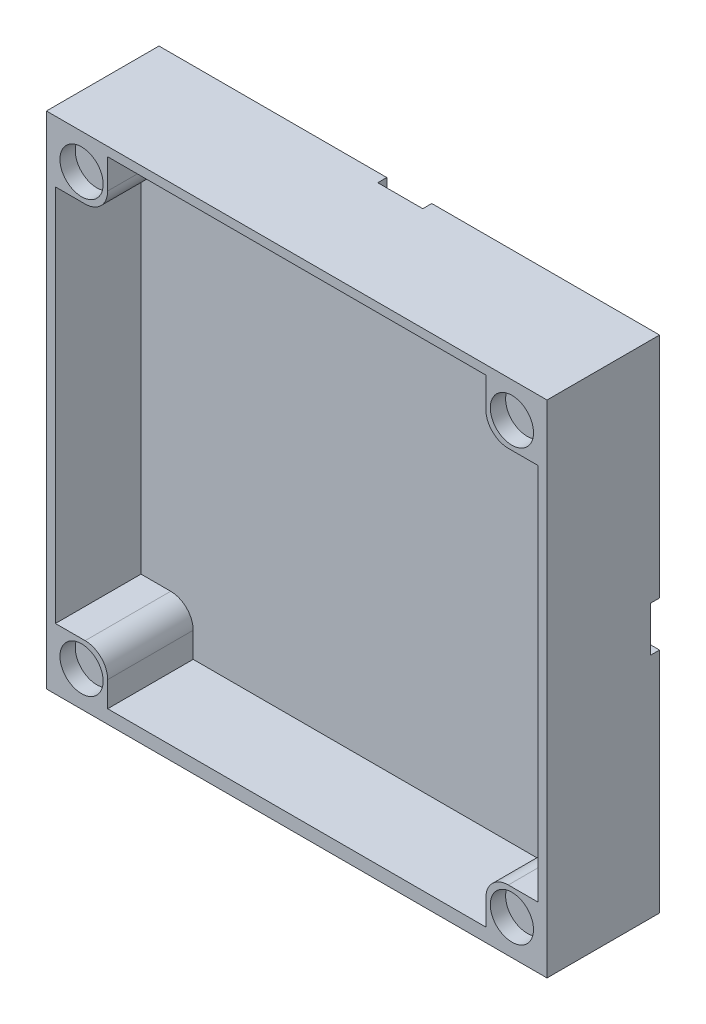
SolidWorks part; units mm, degrees
ref_plane "Přední rovina" through (0, 0, 0) normal (0, 0, 1) x (1, 0, 0)
ref_plane "Horní rovina" through (0, 0, 0) normal (0, 1, 0) x (1, 0, 0)
ref_plane "Pravá rovina" through (0, 0, 0) normal (1, 0, 0) x (0, 0, -1)
sketch "Skica1" plane through (0, 0, 0) normal (0, 0, 1) x (1, 0, 0)
  line L1 (27.8, 27.8) -> (-27.8, 27.8)
  line L2 (27.8, 27.8) -> (27.8, -27.8)
  line L3 (27.8, -27.8) -> (-27.8, -27.8)
  line L4 (-27.8, 27.8) -> (-27.8, -27.8)
  line L5 (27.8, 27.8) -> (-27.8, -27.8) construction
  line L6 (27.8, -27.8) -> (-27.8, 27.8) construction
  point P0 (0, 0)
  point P5 (-27.5, 0)
  point P11 (4.5, 0)
  dimension "D1" = 55.6
  dimension "D2" = 55.6
extrude "Přidat vysunutím2" add sketch "Skica1" along normal blind 3 contours L2 L1 L4 L3
sketch "Skica5" plane through (0, 0, 0) normal (0, 0, -1) x (-1, 0, 0)
  line L0 (-27.8, 27.8) -> (-27.8, -27.8) construction
  line L5 (-27.8, 2.5) -> (2.5, 2.5)
  line L15 (-27.8, 2.5) -> (-27.8, -2.5)
  line L16 (-27.8, -2.5) -> (2.5, -2.5)
  line L17 (2.5, 2.5) -> (2.5, -2.5)
  line L18 (-27.8, 27.8) -> (27.8, 27.8) construction
  line L19 (-27.8, -27.8) -> (27.8, -27.8) construction
  line L21 (2.5, 2.5) -> (-2.5, 2.5)
  line L22 (2.5, 2.5) -> (2.5, 27.8)
  line L23 (2.5, 27.8) -> (-2.5, 27.8)
  line L24 (-2.5, 2.5) -> (-2.5, 27.8)
  point P0 (0, 0)
  dimension "D1" = 5
  dimension "D2" = 30.3
  dimension "D3" = 25.3
  dimension "D4" = 25.3
  dimension "D5" = 25.3
  dimension "D6" = 5
extrude "Odebrat vysunutím3" cut sketch "Skica5" against normal blind 1 contours L17 L5 L15 L16 | L22 L21 L24 L23
sketch "Skica14" plane through (0, 0, 3) normal (0, 0, 1) x (1, 0, 0)
  line L1 (-27.8, 27.8) -> (27.8, 27.8)
  line L2 (-27.8, 27.8) -> (-27.8, -27.8)
  line L3 (-27.8, -27.8) -> (27.8, -27.8)
  line L4 (27.8, 27.8) -> (27.8, -27.8)
  line L5 (-26.8, 26.8) -> (26.8, 26.8)
  line L6 (-26.8, 26.8) -> (-26.8, -27.8)
  line L7 (-26.8, -27.8) -> (26.8, -27.8)
  line L8 (26.8, 26.8) -> (26.8, -27.8)
  line L9 (-26.8, -27.8) -> (26.8, -27.8)
  line L10 (-26.8, -27.8) -> (-26.8, -26.8)
  line L12 (26.8, -27.8) -> (26.8, -26.3)
  line L13 (-26.8, -27.8) -> (26.8, -27.8)
  line L14 (-26.8, -27.8) -> (-26.8, -26.3)
  line L15 (-26.8, -26.3) -> (26.8, -26.3)
  line L16 (26.8, -27.8) -> (26.8, -26.3)
  line M13 (-27.8, -27.8) -> (27.8, -27.8)
  line M14 (27.8, -27.8) -> (27.8, 27.8)
  line M15 (27.8, 27.8) -> (-27.8, 27.8)
  line M16 (-27.8, 27.8) -> (-27.8, -27.8)
  dimension "D1" = 1
  dimension "D2" = 1
  dimension "D3" = 1
  dimension "D4" = 0
  dimension "D5" = 1
  dimension "D6" = 53.6
extrude "Přidat vysunutím9" add sketch "Skica14" along normal blind 9.5 contours L5 L8 L6 M13 M14 M15 M16 | L14 L13 L16 L15
sketch "Skica17" plane through (0, 0, 1) normal (0, 0, -1) x (-1, 0, 0)
  line L0 (-27.8, 2.5) -> (-27.8, -2.5) construction
  line L3 (2.5, 27.8) -> (27.8, 27.8) construction
  line L4 (-2.5, 2.5) -> (-2.5, 27.8) construction
  circle A0 centre (-20.8, 0) radius 2
  circle A1 centre (0, 20.8) radius 2
  dimension "D1" = 4
  dimension "D2" = 4
  dimension "D3" = 7
  dimension "D4" = 7
  dimension "D5" = 2.5
extrude "Odebrat vysunutím8" cut sketch "Skica17" against normal blind 4
sketch "Skica19" plane through (0, 0, 0) normal (0, 0, -1) x (-1, 0, 0)
  line L1 (-27.8, 27.8) -> (-21, 27.8)
  line L2 (-27.8, 27.8) -> (-27.8, 21)
  line L3 (-27.8, 21) -> (-21, 21)
  line L4 (-21, 27.8) -> (-21, 21)
  line L5 (27.8, 27.8) -> (21, 27.8)
  line L6 (27.8, 27.8) -> (27.8, 21)
  line L7 (27.8, 21) -> (21, 21)
  line L8 (21, 27.8) -> (21, 21)
  line L9 (-27.8, -27.8) -> (-21, -27.8)
  line L10 (-27.8, -27.8) -> (-27.8, -21)
  line L11 (-27.8, -21) -> (-21, -21)
  line L12 (-21, -27.8) -> (-21, -21)
  line L13 (27.8, -27.8) -> (21, -27.8)
  line L14 (27.8, -27.8) -> (27.8, -21)
  line L15 (27.8, -21) -> (21, -21)
  line L16 (21, -27.8) -> (21, -21)
  dimension "D1" = 6.8
  dimension "D2" = 6.8
  dimension "D3" = 6.8
  dimension "D4" = 6.8
extrude "Přidat vysunutím10" add sketch "Skica19" against normal blind 12.5
sketch "Skica20" plane through (0, 0, 12.5) normal (0, 0, 1) x (1, 0, 0)
  line L0 (-27.8, -27.8) -> (27.8, -27.8) construction
  line L2 (-27.8, 27.8) -> (-27.8, -27.8) construction
  line L3 (27.8, 27.8) -> (-27.8, 27.8) construction
  line L4 (27.8, -27.8) -> (27.8, 27.8) construction
  line L5 (-27.8, -27.8) -> (27.8, -27.8) construction
  circle A0 centre (-23.9, -23.9) radius 2.4
  circle A1 centre (-23.9, 23.9) radius 2.4
  circle A2 centre (23.9003, 23.9) radius 2.4
  circle A3 centre (23.9003, -23.9) radius 2.4
  dimension "D1" = 4.8
  dimension "D4" = 4.8
  dimension "D5" = 3.9
  dimension "D7" = 4.8
  dimension "D10" = 4.8
  dimension "D2" = 3.9
  dimension "D3" = 3.9
  dimension "D6" = 3.9
  dimension "D8" = 3.8997
  dimension "D9" = 3.9
  dimension "D11" = 3.9
  dimension "D12" = 3.8997
extrude "Odebrat vysunutím9" cut sketch "Skica20" against normal blind 1.7
fillet "Zaoblit1" radius 2.5 4 edges at (21, 21, 7.75) (21, -21, 7.75) (-21, -21, 7.75) (-21, 21, 7.75)
fillet "Zaoblit2" radius 15 1 edges at (2.5, 2.5, 0.5)
fillet "Zaoblit3" radius 20 1 edges at (-2.5, -2.5, 0.5)
